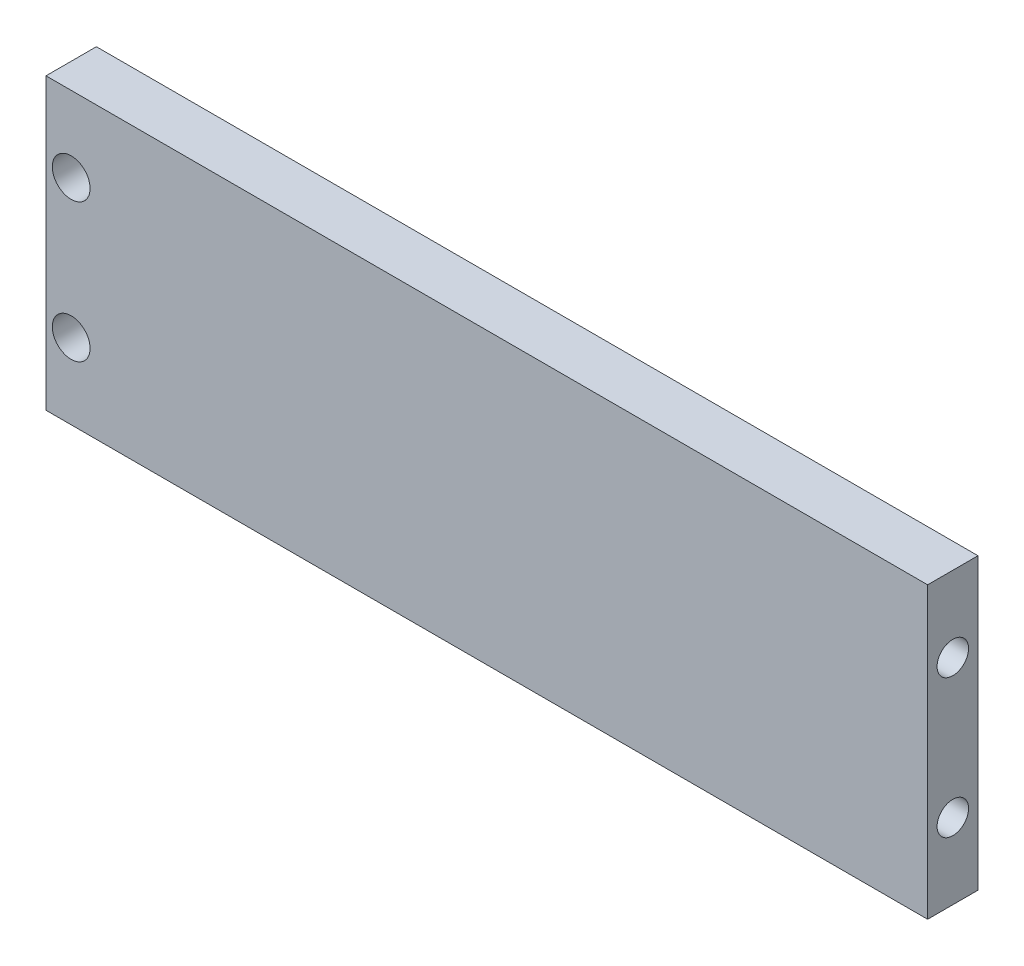
SolidWorks part; units mm, degrees
material "7075-T6 (SN)"
ref_plane "Plano frontal" through (0, 0, 0) normal (0, 0, 1) x (1, 0, 0)
ref_plane "Plano superior" through (0, 0, 0) normal (0, 1, 0) x (1, 0, 0)
ref_plane "Plano direito" through (0, 0, 0) normal (1, 0, 0) x (0, 0, -1)
sketch "Esboço1" plane through (0, 0, 0) normal (0, 0, 1) x (1, 0, 0)
  line L1 (0, 0) -> (70, 0)
  line L2 (0, 0) -> (0, -23)
  line L3 (0, -23) -> (70, -23)
  line L4 (70, 0) -> (70, -23)
  dimension "D1" = 23
  dimension "D2" = 70
extrude "Ressalto-extrusão1" add sketch "Esboço1" along normal blind 4
sketch "Esboço2" plane through (70, 0, 0) normal (1, 0, 0) x (0, 0, -1)
  line L0 (-2, 0) -> (-2, -23) construction
  line L1 (-4, 0) -> (0, 0) construction
  line L2 (-4, -23) -> (0, -23) construction
  circle A0 centre (-2, -6) radius 1.25
  circle A1 centre (-2, -17) radius 1.25
  dimension "D1" = 2.5
  dimension "D2" = 2.5
  dimension "D3" = 6
  dimension "D4" = 6
extrude "Corte-extrusão1" cut sketch "Esboço2" against normal blind 10
sketch "Esboço3" plane through (0, -23, 0) normal (0, -1, 0) x (-1, 0, 0)
  line L0 (0, -2) -> (-70, -2) construction
  line L1 (0, -4) -> (0, 0) construction
  line L2 (-70, -4) -> (-70, 0) construction
  circle A0 centre (-15, -2) radius 1.25
  circle A1 centre (-35, -2) radius 1.25
  circle A2 centre (-55, -2) radius 1.25
  dimension "D1" = 2.5
  dimension "D4" = 2.5
  dimension "D5" = 2.5
  dimension "D2" = 15
  dimension "D3" = 15
extrude "Corte-extrusão2" cut sketch "Esboço3" against normal blind 10
sketch "Esboço4" plane through (0, 0, 4) normal (0, 0, 1) x (1, 0, 0)
  line L0 (2, 0) -> (2, -23) construction
  line L1 (70, 0) -> (0, 0) construction
  line L2 (0, -23) -> (70, -23) construction
  line L3 (0, 0) -> (0, -23) construction
  circle A0 centre (2, -6) radius 1.5
  circle A1 centre (2, -17) radius 1.5
  dimension "D2" = 3
  dimension "D3" = 3
  dimension "D1" = 2
  dimension "D4" = 6
  dimension "D5" = 6
extrude "Corte-extrusão3" cut sketch "Esboço4" against normal blind 10
